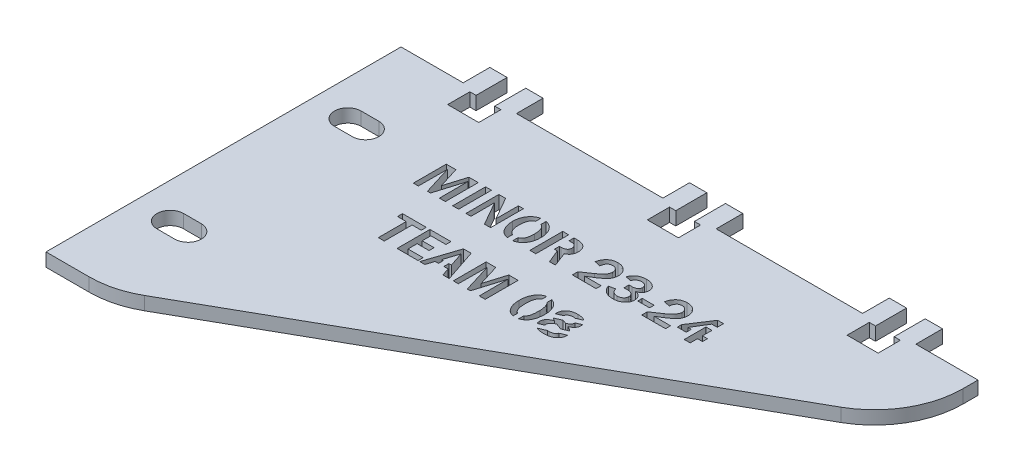
SolidWorks part; units mm, degrees
ref_plane "Front Plane" through (0, 0, 0) normal (0, 0, 1) x (1, 0, 0)
ref_plane "Top Plane" through (0, 0, 0) normal (0, 1, 0) x (1, 0, 0)
ref_plane "Right Plane" through (0, 0, 0) normal (1, 0, 0) x (0, 0, -1)
sketch "Sketch1" plane through (0, 0, 0) normal (0, 1, 0) x (1, 0, 0)
  line L0 (0, 0) -> (130, 0)
  line L2 (0, -80) -> (0, 0)
  line L3 (130, 0) -> (130, -15)
  line L4 (104, 6) -> (116, 6)
  line L5 (104, 6) -> (104, 0)
  line L6 (104, 0) -> (116, 0)
  line L7 (116, 6) -> (116, 0)
  line L8 (104, 6) -> (116, 0) construction
  line L9 (104, 0) -> (116, 6) construction
  line L10 (59, 6) -> (71, 6)
  line L11 (59, 6) -> (59, 0)
  line L12 (59, 0) -> (71, 0)
  line L13 (71, 6) -> (71, 0)
  line L14 (59, 6) -> (71, 0) construction
  line L15 (59, 0) -> (71, 6) construction
  line L16 (14, 6) -> (26, 6)
  line L17 (14, 6) -> (14, 0)
  line L18 (14, 0) -> (26, 0)
  line L19 (26, 6) -> (26, 0)
  line L20 (14, 6) -> (26, 0) construction
  line L21 (14, 0) -> (26, 6) construction
  line L22 (130, -15) -> (15, -80)
  line L23 (15, -80) -> (0, -80)
  point P4 (110, 3)
  point P9 (65, 3)
  point P14 (20, 3)
  dimension "D1" = 130
  dimension "D2" = 80
  dimension "D3" = 12
  dimension "D4" = 6
  dimension "D5" = 20
  dimension "D6" = 45
  dimension "D7" = 45
  dimension "D8" = 15
  dimension "D9" = 15
extrude "Boss-Extrude1" add sketch "Sketch1" along normal blind 3 contours L2 L0 L3 L22 L23 | L17 L16 L19 L18 | L11 L10 L13 L12 | L5 L4 L7 L6
sketch "Sketch2" plane through (0, 3, 0) normal (0, 1, 0) x (1, 0, 0)
  line L0 (8, -20) -> (12, -20) construction
  line L1 (8, -17) -> (12, -17)
  line L2 (8, -23) -> (12, -23)
  line L3 (8, -60) -> (12, -60) construction
  line L4 (8, -57) -> (12, -57)
  line L5 (8, -63) -> (12, -63)
  line L6 (0, 0) -> (14, 0) construction
  line L8 (0, -80) -> (0, 0) construction
  arc A0 (8, -17) -> (8, -23) centre (8, -20) ccw
  arc A1 (12, -23) -> (12, -17) centre (12, -20) ccw
  arc A2 (8, -57) -> (8, -63) centre (8, -60) ccw
  arc A3 (12, -63) -> (12, -57) centre (12, -60) ccw
  point P2 (10, -20)
  point P7 (10, -60)
  point P19 (10, -17)
  dimension "D5" = 6
  dimension "D6" = 8
  dimension "D1" = 20
  dimension "D2" = 40
  dimension "D3" = 4
  dimension "D4" = 4
  dimension "D7" = 6
extrude "Cut-Extrude1" cut sketch "Sketch2" against normal blind 10
sketch "Sketch3" plane through (0, 3, 0) normal (0, 1, 0) x (1, 0, 0)
  line L0 (59, 6) -> (71, 6) construction
  line L1 (62.9, 6) -> (67.1, 6)
  line L2 (62.9, 6) -> (62.9, -1)
  line L3 (62.9, -1) -> (67.1, -1)
  line L4 (67.1, 6) -> (67.1, -1)
  line L5 (62.9, 6) -> (67.1, -1) construction
  line L6 (62.9, -1) -> (67.1, 6) construction
  line L7 (61.5, -6) -> (68.5, -6)
  line L8 (61.5, -6) -> (61.5, -1)
  line L9 (61.5, -1) -> (68.5, -1)
  line L10 (68.5, -6) -> (68.5, -1)
  line L11 (61.5, -6) -> (68.5, -1) construction
  line L12 (61.5, -1) -> (68.5, -6) construction
  line L16 (17.9, 6) -> (22.1, 6)
  line L17 (17.9, 6) -> (17.9, -1)
  line L18 (17.9, -1) -> (22.1, -1)
  line L19 (22.1, 6) -> (22.1, -1)
  line L20 (17.9, 6) -> (22.1, -1) construction
  line L21 (17.9, -1) -> (22.1, 6) construction
  line L22 (16.5, -6) -> (23.5, -6)
  line L23 (16.5, -6) -> (16.5, -1)
  line L24 (16.5, -1) -> (23.5, -1)
  line L25 (23.5, -6) -> (23.5, -1)
  line L26 (16.5, -6) -> (23.5, -1) construction
  line L27 (16.5, -1) -> (23.5, -6) construction
  line L29 (107.9, 6) -> (112.1, 6)
  line L30 (107.9, 6) -> (107.9, -1)
  line L31 (107.9, -1) -> (112.1, -1)
  line L32 (112.1, 6) -> (112.1, -1)
  line L33 (107.9, 6) -> (112.1, -1) construction
  line L34 (107.9, -1) -> (112.1, 6) construction
  line L35 (106.5, -6) -> (113.5, -6)
  line L36 (106.5, -6) -> (106.5, -1)
  line L37 (106.5, -1) -> (113.5, -1)
  line L38 (113.5, -6) -> (113.5, -1)
  line L39 (106.5, -6) -> (113.5, -1) construction
  line L40 (106.5, -1) -> (113.5, -6) construction
  line L41 (14, 6) -> (26, 6) construction
  line L42 (104, 6) -> (116, 6) construction
  point P0 (65, 2.5)
  point P5 (65, -3.5)
  point P13 (65, 6)
  point P16 (65, 6)
  point P17 (20, 2.5)
  point P22 (20, -3.5)
  point P27 (20, 6)
  point P28 (110, 2.5)
  point P36 (110, -3.5)
  point P41 (110, 6)
  point P42 (20, 6)
  point P45 (110, 6)
  line M22 (116, 6) -> (104, 6)
  line M26 (71, 6) -> (59, 6)
  line M30 (26, 6) -> (14, 6)
  dimension "D1" = 4.2
  dimension "D2" = 7
  dimension "D3" = 5
  dimension "D4" = 7
  dimension "D5" = 4.2
  dimension "D6" = 7
  dimension "D7" = 5
  dimension "D8" = 7
  dimension "D9" = 4.2
  dimension "D10" = 7
  dimension "D11" = 5
  dimension "D12" = 7
extrude "Cut-Extrude2" cut sketch "Sketch3" against normal blind 10 contours L7 L10 L9 L3 L8 | L4 L2 L3 M26 | L19 L17 L18 M30 | L22 L25 L24 L18 L23 | L32 L30 L31 M22 | L35 L38 L37 L31 L36
fillet "Fillet1" radius 20 2 edges at (15, 1.5, 80) (130, 1.5, 15)
sketch "Sketch5" plane through (0, 3, 0) normal (0, 1, 0) x (1, 0, 0)
  text T0 "MINOR 23-24\r\n  TEAM 08" font "Franklin Gothic Medium" height in points 30
extrude "Cut-Extrude3" cut sketch "Sketch5" against normal through all both and the other way through all
sketch "Sketch6" plane through (0, 3, 0) normal (0, 1, 0) x (1, 0, 0)
  line L0 (57.3962, -17.7767) -> (54.2105, -17.7767) construction
  line L1 (49.1894, -17.0422) -> (50.3894, -17.0422)
  line L2 (49.1894, -17.0422) -> (49.1894, -26.2957)
  line L3 (49.1894, -26.2957) -> (50.3894, -26.2957)
  line L4 (50.3894, -17.0422) -> (50.3894, -26.2957)
  line L5 (55.5484, -22.2024) -> (56.7484, -22.2024)
  line L6 (55.5484, -22.2024) -> (55.5484, -17.7767)
  line L7 (55.5484, -17.7767) -> (56.7484, -17.7767)
  line L8 (56.7484, -22.2024) -> (56.7484, -17.7767)
  line L19 (89.0963, -19.089) -> (90.3362, -19.089)
  line L20 (90.3362, -22.4082) -> (90.3362, -17.6738) construction
  line L21 (90.3362, -19.089) -> (90.3362, -20.289)
  line L22 (90.3362, -20.289) -> (88.366, -20.289)
  line L23 (87.0764, -22.4082) -> (89.0963, -19.089) construction
  line L24 (88.366, -20.289) -> (89.0963, -19.089)
  line L25 (88.9982, -23.5404) -> (87.7982, -23.5404)
  line L26 (85.8076, -23.5404) -> (88.9982, -23.5404) construction
  line L27 (87.7982, -23.5404) -> (87.7982, -22.4082)
  line L28 (88.9982, -22.4082) -> (87.0764, -22.4082) construction
  line L29 (87.7982, -22.4082) -> (88.9982, -22.4082)
  line L30 (88.9982, -22.4082) -> (88.9982, -23.5404)
  line L31 (45.7129, -38.0232) -> (48.6253, -38.0232) construction
  line L32 (46.4605, -36.4372) -> (47.6605, -36.4372)
  line L33 (46.4605, -36.4372) -> (46.4605, -38.0232)
  line L34 (46.4605, -38.0232) -> (47.6605, -38.0232)
  line L35 (47.6605, -36.4372) -> (47.6605, -38.0232)
  line L36 (69.1593, -34.8281) -> (75.0673, -32.2391)
  line L37 (65.104, -31.1515) -> (66.304, -31.1515)
  line L38 (65.104, -31.1515) -> (65.104, -41.2047)
  line L39 (65.104, -41.2047) -> (66.304, -41.2047)
  line L40 (66.304, -31.1515) -> (66.304, -41.2047)
  line L41 (75.0673, -32.2391) -> (75.549, -33.3382)
  line L42 (75.549, -33.3382) -> (69.641, -35.9272)
  line L43 (69.641, -35.9272) -> (69.1593, -34.8281)
  line L44 (69.266, -39.9283) -> (76.8851, -36.7104)
  line L45 (76.8851, -36.7104) -> (76.4182, -35.605)
  line L46 (76.4182, -35.605) -> (68.7991, -38.8229)
  line L47 (68.7991, -38.8229) -> (69.266, -39.9283)
  dimension "D1" = 1.2
  dimension "D2" = 1.2
  dimension "D3" = 1.2
  dimension "D4" = 1.2
  dimension "D5" = 1.2
  dimension "D6" = 1.2
  dimension "D7" = 1.2
  dimension "D8" = 1.2
extrude "Boss-Extrude2" add sketch "Sketch6" against normal up to surface (3 mm away) up to face at (57.0967, 0, 22.0562)
